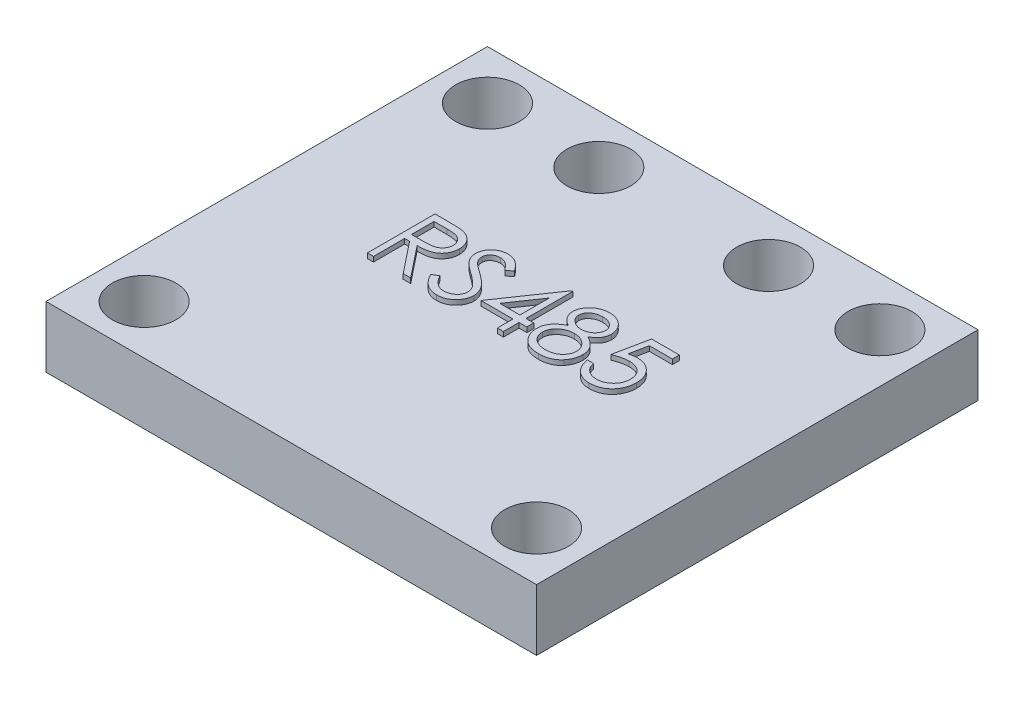
SolidWorks part; units mm, degrees
ref_plane "Front Plane" through (0, 0, 0) normal (0, 0, 1) x (1, 0, 0)
ref_plane "Top Plane" through (0, 0, 0) normal (0, 1, 0) x (1, 0, 0)
ref_plane "Right Plane" through (0, 0, 0) normal (1, 0, 0) x (0, 0, -1)
sketch "Sketch2" plane through (0, 0, 0) normal (0, 1, 0) x (1, 0, 0)
  line L1 (-12.7, 11.43) -> (12.7, 11.43)
  line L2 (-12.7, 11.43) -> (-12.7, -11.43)
  line L3 (-12.7, -11.43) -> (12.7, -11.43)
  line L4 (12.7, 11.43) -> (12.7, -11.43)
  line L5 (-12.7, 11.43) -> (12.7, -11.43) construction
  line L6 (-12.7, -11.43) -> (12.7, 11.43) construction
  circle A0 centre (-10.16, 8.89) radius 1.651
  circle A1 centre (10.16, 8.89) radius 1.651
  circle A2 centre (10.16, -8.89) radius 1.651
  circle A3 centre (-10.16, -8.89) radius 1.651
  circle A4 centre (-4.3942, 8.89) radius 1.651
  circle A5 centre (4.3942, 8.89) radius 1.651
  point P0 (0, 0)
  point P18 (0, 0)
  dimension "D3" = 3.302
  dimension "D9" = 2.54
  dimension "D11" = 3.302
  dimension "D12" = 3.302
  dimension "D1" = 25.4
  dimension "D2" = 22.86
  dimension "D4" = 2.54
  dimension "D5" = 2.54
  dimension "D8" = 2.54
  dimension "D10" = 20.32
  dimension "D13" = 5.7658
  dimension "D14" = 5.7658
  dimension "D15" = 2.54
  dimension "D16" = 2.54
  dimension "D6" = 2
  dimension "D7" = 2
extrude "Boss-Extrude1" add sketch "Sketch2" against normal blind 3.175
sketch "Sketch3" plane through (0, 0, 0) normal (0, 1, 0) x (1, 0, 0)
  text T0 "RS485 " font "Century Gothic" height 3.5
extrude "Boss-Extrude2" add sketch "Sketch3" along normal blind 0.254
